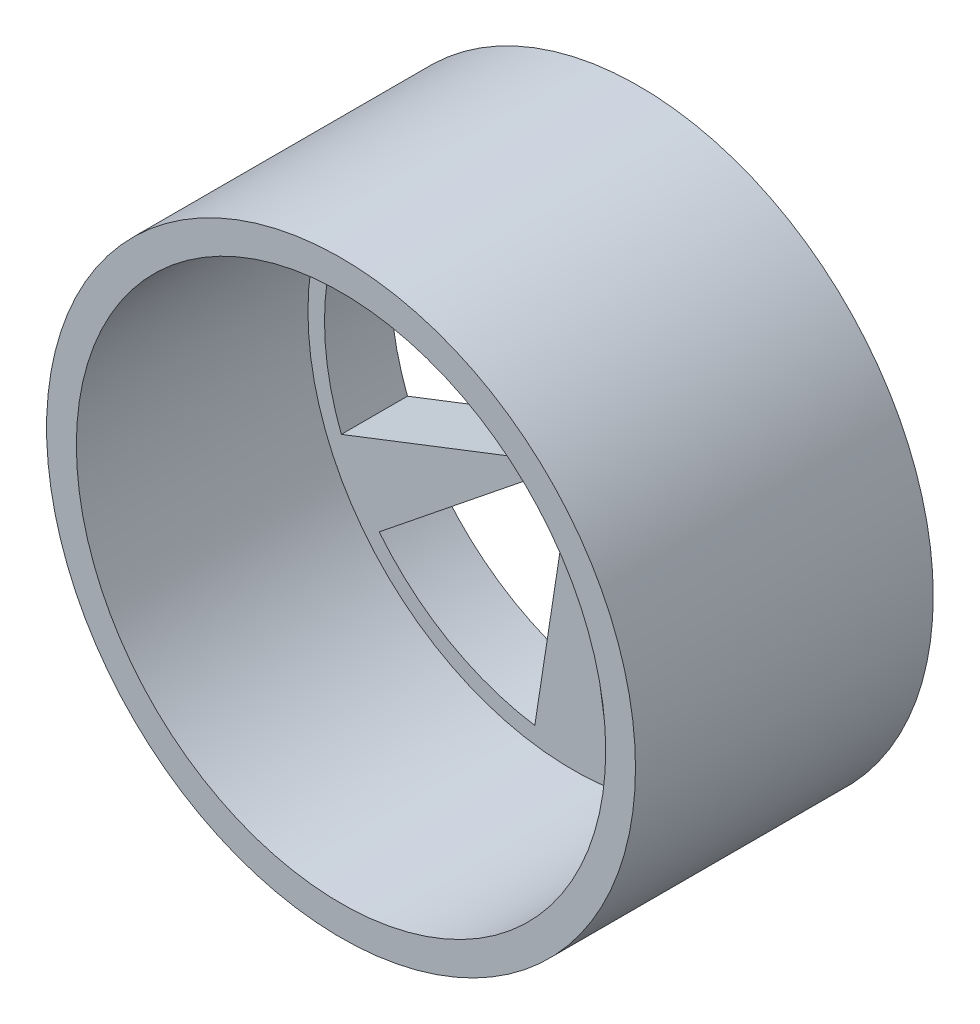
SolidWorks part; units mm, degrees
material "AISI 316 Stainless Steel Sheet (SS)"
ref_plane "Front Plane" through (0, 0, 0) normal (0, 0, 1) x (1, 0, 0)
ref_plane "Top Plane" through (0, 0, 0) normal (0, 1, 0) x (1, 0, 0)
ref_plane "Right Plane" through (0, 0, 0) normal (1, 0, 0) x (0, 0, -1)
sketch "Sketch1" plane through (0, 0, 0) normal (0, 0, 1) x (1, 0, 0)
  arc A0 (336.6581, 0) -> (128.812, 0) centre (232.735, 15) ccw construction
  arc A1 (336.6581, 0) -> (128.812, 0) centre (232.735, 15) ccw
  circle A2 centre (232.735, 15) radius 89
  dimension "D1" = 16
extrude "Boss-Extrude1" add sketch "Sketch1" against normal blind 90 contours A2
sketch "Sketch2" plane through (0, 0, 0) normal (0, 0, 1) x (1, 0, 0)
  line L0 (232.735, 90) -> (232.735, 30) construction
  line L1 (221.3019, 89.1234) -> (230.4484, 29.8247)
  line L2 (244.1681, 89.1234) -> (235.0216, 29.8247)
  line L3 (162.8257, 42.1604) -> (218.7532, 20.4321)
  line L4 (174.2588, 61.9631) -> (221.0398, 24.3926)
  line L5 (174.2588, -31.9631) -> (221.0398, 5.6074)
  line L6 (162.8257, -12.1604) -> (218.7532, 9.5679)
  line L7 (244.1681, -59.1234) -> (235.0216, 0.1753)
  line L8 (221.3019, -59.1234) -> (230.4484, 0.1753)
  line L9 (302.6444, -12.1604) -> (246.7169, 9.5679)
  line L10 (291.2113, -31.9631) -> (244.4303, 5.6074)
  line L11 (291.2113, 61.9631) -> (244.4303, 24.3926)
  line L12 (302.6444, 42.1604) -> (246.7169, 20.4321)
  arc A0 (162.8257, 42.1604) -> (162.8257, -12.1604) centre (232.735, 15) ccw
  circle A1 centre (232.735, 15) radius 89 construction
  arc A2 (218.7532, 20.4321) -> (218.7532, 9.5679) centre (232.735, 15) ccw
  arc A3 (221.3019, 89.1234) -> (174.2588, 61.9631) centre (232.735, 15) ccw
  arc A4 (230.4484, 29.8247) -> (221.0398, 24.3926) centre (232.735, 15) ccw
  arc A5 (244.4303, 24.3926) -> (235.0216, 29.8247) centre (232.735, 15) ccw
  arc A6 (291.2113, 61.9631) -> (244.1681, 89.1234) centre (232.735, 15) ccw
  arc A7 (302.6444, -12.1604) -> (302.6444, 42.1604) centre (232.735, 15) ccw
  arc A8 (246.7169, 9.5679) -> (246.7169, 20.4321) centre (232.735, 15) ccw
  arc A9 (235.0216, 0.1753) -> (244.4303, 5.6074) centre (232.735, 15) ccw
  arc A10 (244.1681, -59.1234) -> (291.2113, -31.9631) centre (232.735, 15) ccw
  arc A11 (174.2588, -31.9631) -> (221.3019, -59.1234) centre (232.735, 15) ccw
  arc A12 (221.0398, 5.6074) -> (230.4484, 0.1753) centre (232.735, 15) ccw
  point P33 (232.735, 15)
  dimension "D1" = 150
  dimension "D2" = 30
  dimension "D3" = 59.2988
  dimension "D4" = 6
extrude "Cut-Extrude1" cut sketch "Sketch2" against normal through all
sketch "Sketch3" plane through (0, 0, 0) normal (0, 0, 1) x (1, 0, 0)
  circle A0 centre (232.735, 15) radius 80
  circle A1 centre (232.735, 15) radius 89 construction
  dimension "D1" = 160
extrude "Cut-Extrude2" cut sketch "Sketch3" against normal blind 70
sketch "Sketch4" plane through (0, 0, -90) normal (0, 0, -1) x (-1, 0, 0)
  circle A0 centre (-232.735, 15) radius 10
  arc A1 (-235.0216, 29.8247) -> (-244.4303, 24.3926) centre (-232.735, 15) ccw construction
  dimension "D1" = 20
extrude "Cut-Extrude3" cut sketch "Sketch4" against normal through all
